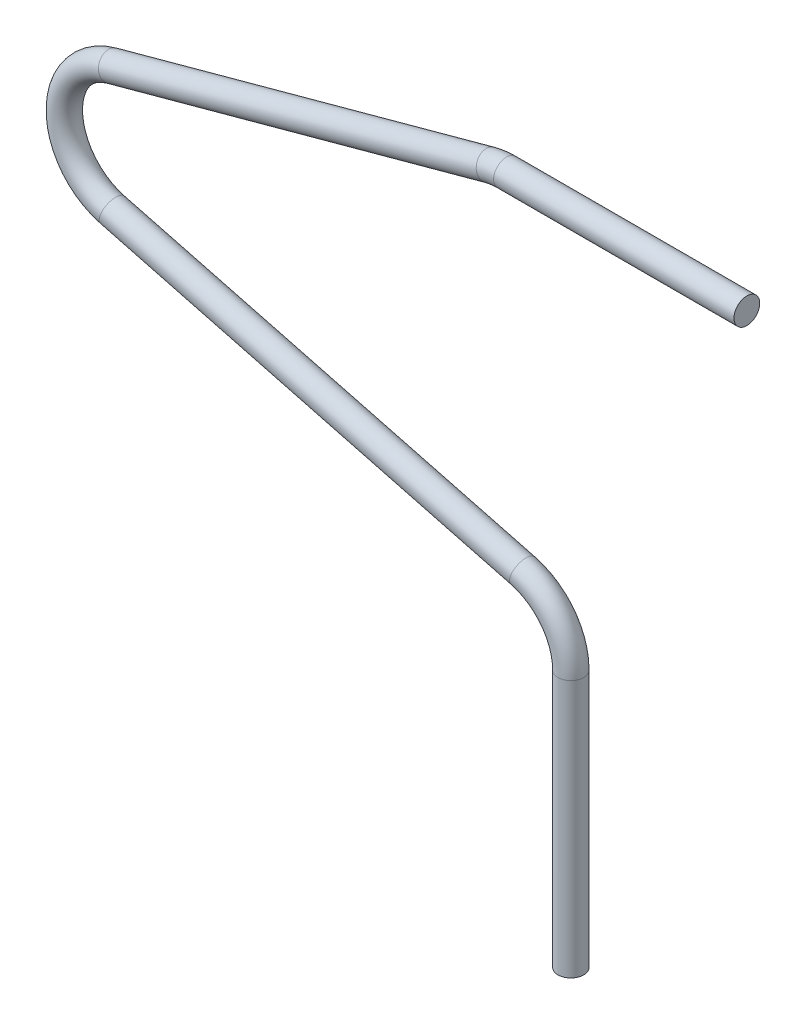
SolidWorks part; units mm, degrees
ref_plane "Vorne" through (0, 0, 0) normal (0, 0, 1) x (1, 0, 0)
ref_plane "Oben" through (0, 0, 0) normal (0, 1, 0) x (1, 0, 0)
ref_plane "Rechts" through (0, 0, 0) normal (1, 0, 0) x (0, 0, -1)
sketch "Skizze1" plane through (0, 0, 0) normal (0, 0, 1) x (1, 0, 0)
  line L0 (0, 0) -> (0, 15)
  line L1 (-2.802, 18.6282) -> (-26.698, 24.8718)
  line L2 (-26.7367, 32.1179) -> (-4.7367, 38.1179)
  line L3 (-3.75, 38.25) -> (10.25, 38.25)
  line L4 (-25.75, 25.5) -> (-3.75, 25.5) construction
  line L5 (-3.75, 25.5) -> (-3.75, 18) construction
  line L6 (-25.75, 31.5) -> (-25.75, 37.5) construction
  line L7 (-25.75, 37.5) -> (-3.75, 37.5) construction
  arc A0 (0, 15) -> (-2.802, 18.6282) centre (-3.75, 15) ccw
  arc A1 (-26.698, 24.8718) -> (-26.7367, 32.1179) centre (-25.75, 28.5) cw
  arc A2 (-4.7367, 38.1179) -> (-3.75, 38.25) centre (-3.75, 34.5) cw
  circle A3 centre (-25.75, 28.5) radius 3.75 construction
  circle A4 centre (-3.75, 34.5) radius 3.75 construction
  circle A5 centre (-3.75, 15) radius 3.75 construction
  circle A6 centre (-25.75, 28.5) radius 3 construction
  circle A7 centre (-3.75, 15) radius 3 construction
  circle A8 centre (-3.75, 34.5) radius 3 construction
  dimension "D1" = 6
  dimension "D2" = 6
  dimension "D3" = 7.5
  dimension "D7" = 6
  dimension "D8" = 7.5
  dimension "D4" = 22
  dimension "D5" = 15
  dimension "D6" = 14
  dimension "D9" = 6
sketch "Skizze2" plane through (0, 0, 0) normal (0, 1, 0) x (1, 0, 0)
  circle A0 centre (0, 0) radius 0.75
  dimension "D1" = 1.5
sweep "Austragung1" add profiles "Skizze2" path "Skizze1"
move or copy body "Körper-Verschieben/Kopieren1" [suppressed] bodies to move or copy 103
